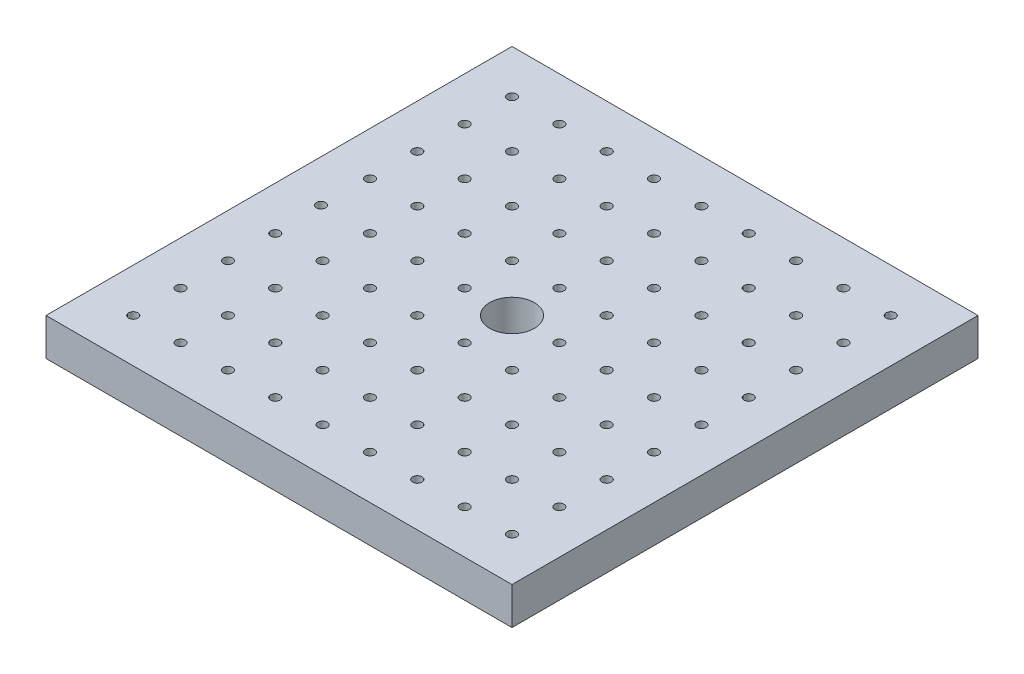
SolidWorks part; units mm, degrees
ref_plane "Front Plane" through (0, 0, 0) normal (0, 0, 1) x (1, 0, 0)
ref_plane "Top Plane" through (0, 0, 0) normal (0, 1, 0) x (1, 0, 0)
ref_plane "Right Plane" through (0, 0, 0) normal (1, 0, 0) x (0, 0, -1)
sketch "스케치1" plane through (0, 0, 0) normal (0, 1, 0) x (1, 0, 0)
  line L1 (-12.5, 12.5) -> (12.5, 12.5)
  line L2 (-12.5, 12.5) -> (-12.5, -12.5)
  line L3 (-12.5, -12.5) -> (12.5, -12.5)
  line L4 (12.5, 12.5) -> (12.5, -12.5)
  dimension "D1" = 25
  dimension "D2" = 25
  dimension "D3" = 12.5
  dimension "D4" = 12.5
extrude "보스-돌출1" add sketch "스케치1" along normal blind 2
sketch "스케치2" plane through (0, 2, 0) normal (0, 1, 0) x (1, 0, 0)
  circle A0 centre (0, 0) radius 1.2
extrude "컷-돌출1" cut sketch "스케치2" against normal blind 2
sketch "스케치3" plane through (0, 2, 0) normal (0, 1, 0) x (1, 0, 0)
  line L0 (0, 0) -> (0, -50000) construction
  line L1 (0, 0) -> (50000, 0) construction
  line L2 (-2.54, 0) -> (-2.54, -50000) construction
  line L3 (-5.08, 0) -> (-5.08, -50000) construction
  line L4 (-7.62, 0) -> (-7.62, -50000) construction
  line L5 (-10.16, 0) -> (-10.16, -50000) construction
  line L6 (-12.7, 0) -> (-12.7, -50000) construction
  line L7 (2.54, 0) -> (2.54, -50000) construction
  line L8 (5.08, 0) -> (5.08, -50000) construction
  line L9 (10.16, 0) -> (10.16, 50000) construction
  line L10 (12.7, 0) -> (12.7, 50000) construction
  line L11 (7.62, 0) -> (7.62, -50000) construction
  line L12 (-18.2023, 2.54) -> (49981.7977, 2.54) construction
  line L13 (-18.2993, 5.08) -> (49981.7007, 5.08) construction
  line L14 (-18.4286, 7.62) -> (49981.5714, 7.62) construction
  line L15 (-18.3963, 10.16) -> (49981.6037, 10.16) construction
  line L16 (-19.0429, -2.54) -> (49980.9571, -2.54) construction
  line L17 (-20.9828, -5.08) -> (49979.0172, -5.08) construction
  line L18 (-22.5347, -7.62) -> (49977.4653, -7.62) construction
  line L19 (-23.1166, -10.16) -> (49976.8834, -10.16) construction
  circle A0 centre (0, 0) radius 0.25
  circle A1 centre (-2.54, 0) radius 0.25
  circle A2 centre (-5.08, 0) radius 0.25
  circle A3 centre (-7.62, 0) radius 0.25
  circle A4 centre (-10.2489, 0) radius 0.25
  circle A5 centre (2.54, 0) radius 0.25
  circle A6 centre (5.08, 0) radius 0.25
  circle A7 centre (7.62, 0) radius 0.25
  circle A8 centre (10.16, 0) radius 0.25
  circle A9 centre (-10.16, 2.54) radius 0.25
  circle A10 centre (-7.62, 2.54) radius 0.25
  circle A11 centre (-5.08, 2.54) radius 0.25
  circle A12 centre (-2.54, 2.54) radius 0.25
  circle A13 centre (0, 2.54) radius 0.25
  circle A14 centre (2.54, 2.54) radius 0.25
  circle A15 centre (5.08, 2.54) radius 0.25
  circle A16 centre (7.62, 2.54) radius 0.25
  circle A17 centre (10.16, 2.54) radius 0.25
  circle A18 centre (-10.16, 5.08) radius 0.25
  circle A19 centre (-7.62, 5.08) radius 0.25
  circle A20 centre (-5.08, 5.08) radius 0.25
  circle A21 centre (-2.54, 5.08) radius 0.25
  circle A22 centre (0, 5.08) radius 0.25
  circle A23 centre (2.54, 5.08) radius 0.25
  circle A24 centre (5.08, 5.08) radius 0.25
  circle A25 centre (7.62, 5.08) radius 0.25
  circle A26 centre (10.16, 5.08) radius 0.25
  circle A27 centre (10.16, 7.62) radius 0.25
  circle A28 centre (7.62, 7.62) radius 0.25
  circle A29 centre (5.08, 7.62) radius 0.25
  circle A30 centre (2.54, 7.62) radius 0.25
  circle A31 centre (0, 7.62) radius 0.25
  circle A32 centre (-2.54, 7.62) radius 0.25
  circle A33 centre (-5.08, 7.62) radius 0.25
  circle A34 centre (-7.62, 7.62) radius 0.25
  circle A35 centre (-10.16, 7.62) radius 0.25
  circle A36 centre (10.16, 10.16) radius 0.25
  circle A37 centre (7.62, 10.16) radius 0.25
  circle A38 centre (5.08, 10.16) radius 0.25
  circle A39 centre (2.54, 10.16) radius 0.25
  circle A40 centre (0, 10.16) radius 0.25
  circle A41 centre (-2.54, 10.16) radius 0.25
  circle A42 centre (-5.08, 10.16) radius 0.25
  circle A43 centre (-7.62, 10.16) radius 0.25
  circle A44 centre (-10.16, 10.16) radius 0.25
  circle A45 centre (10.16, -2.54) radius 0.25
  circle A46 centre (7.62, -2.54) radius 0.25
  circle A47 centre (5.08, -2.54) radius 0.25
  circle A48 centre (2.54, -2.54) radius 0.25
  circle A49 centre (0, -2.54) radius 0.25
  circle A50 centre (-2.54, -2.54) radius 0.25
  circle A51 centre (-5.08, -2.54) radius 0.25
  circle A52 centre (-7.62, -2.54) radius 0.25
  circle A53 centre (-10.16, -2.54) radius 0.25
  circle A54 centre (10.16, -5.08) radius 0.25
  circle A55 centre (7.62, -5.08) radius 0.25
  circle A56 centre (5.08, -5.08) radius 0.25
  circle A57 centre (2.54, -5.08) radius 0.25
  circle A58 centre (0, -5.08) radius 0.25
  circle A59 centre (-2.54, -5.08) radius 0.25
  circle A60 centre (-5.08, -5.08) radius 0.25
  circle A61 centre (-7.62, -5.08) radius 0.255
  circle A62 centre (-10.16, -5.08) radius 0.25
  circle A63 centre (-10.16, -7.62) radius 0.25
  circle A64 centre (-7.62, -7.62) radius 0.25
  circle A65 centre (-5.08, -7.62) radius 0.25
  circle A66 centre (-2.54, -7.62) radius 0.25
  circle A67 centre (0, -7.62) radius 0.25
  circle A68 centre (2.54, -7.62) radius 0.25
  circle A69 centre (5.08, -7.62) radius 0.25
  circle A70 centre (7.62, -7.62) radius 0.25
  circle A71 centre (10.16, -7.62) radius 0.25
  circle A72 centre (-10.16, -10.16) radius 0.25
  circle A73 centre (-7.62, -10.16) radius 0.25
  circle A74 centre (-5.08, -10.16) radius 0.25
  circle A75 centre (-2.54, -10.16) radius 0.25
  circle A76 centre (0, -10.16) radius 0.25
  circle A77 centre (2.54, -10.16) radius 0.25
  circle A78 centre (5.08, -10.16) radius 0.25
  circle A79 centre (7.62, -10.16) radius 0.25
  circle A80 centre (10.16, -10.16) radius 0.25
  dimension "D11" = 2.54
  dimension "D19" = 0.5
  dimension "D1" = 2.54
  dimension "D2" = 2.54
  dimension "D3" = 2.54
  dimension "D4" = 2.54
  dimension "D5" = 2.54
  dimension "D6" = 2.54
  dimension "D7" = 2.54
  dimension "D8" = 2.54
  dimension "D9" = 2.54
  dimension "D10" = 2.54
  dimension "D12" = 2.54
  dimension "D13" = 2.54
  dimension "D14" = 2.54
  dimension "D15" = 2.54
  dimension "D16" = 2.54
  dimension "D17" = 2.54
  dimension "D18" = 2.54
extrude "컷-돌출2" cut sketch "스케치3" against normal blind 2
